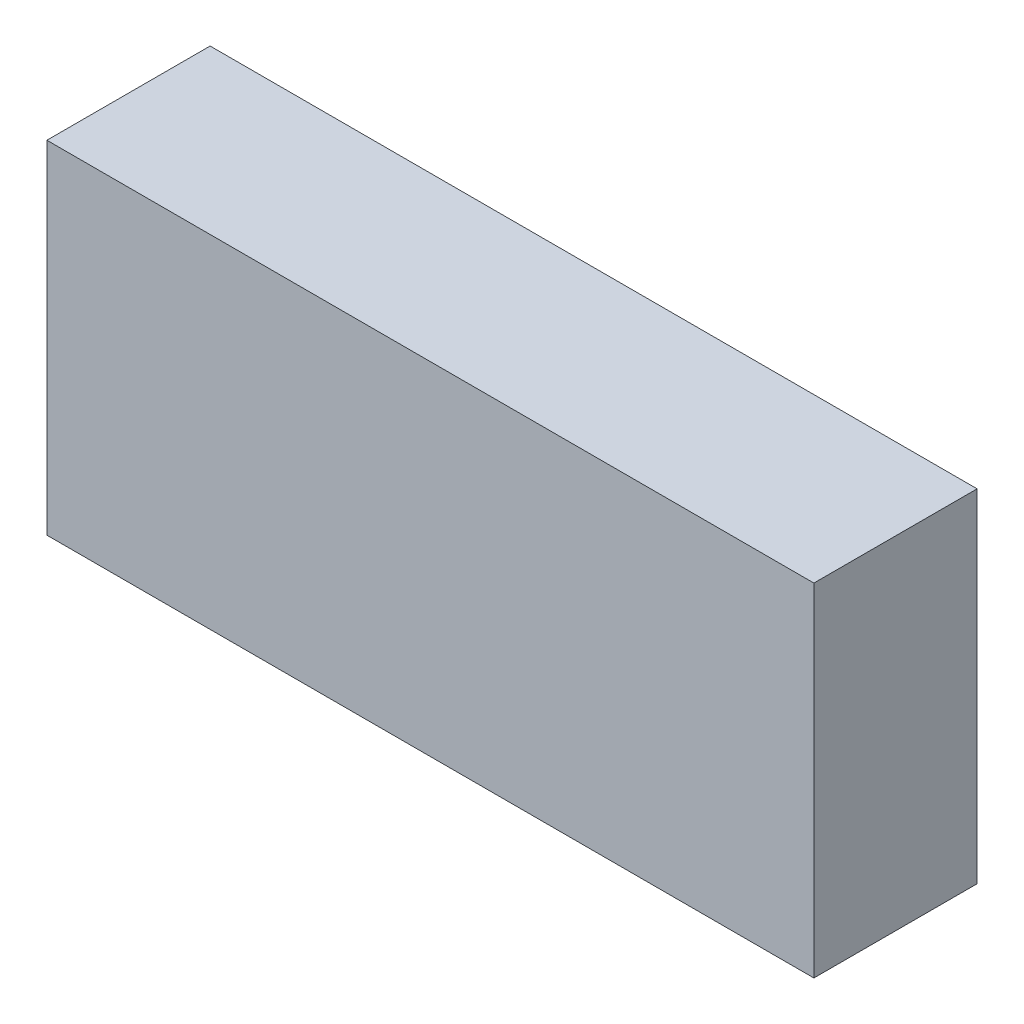
SolidWorks part; units mm, degrees
ref_plane "Front Plane" through (0, 0, 0) normal (0, 0, 1) x (1, 0, 0)
ref_plane "Top Plane" through (0, 0, 0) normal (0, 1, 0) x (1, 0, 0)
ref_plane "Right Plane" through (0, 0, 0) normal (1, 0, 0) x (0, 0, -1)
sketch "Sketch1" plane through (0, 0, 0) normal (0, 0, 1) x (1, 0, 0)
  line L0 (-2.3495, 1.0795) -> (2.3495, 1.0795)
  line L1 (2.3495, 1.0795) -> (2.3495, -1.016)
  line L2 (2.3495, -1.016) -> (-2.3495, -1.016)
  line L3 (-2.3495, -1.016) -> (-2.3495, 1.0795)
extrude "Component_Outline" add sketch "Sketch1" along normal blind 1 separate body
sketch3d "3DSketch1"
  line L0 (0, 0, 0) -> (1, 0, 0)
  line L1 (0, 0, 0) -> (0, 1, 0)
  line L2 (0, 0, 0) -> (0, 0, 1)
  point P0 (0, 0, 0)
